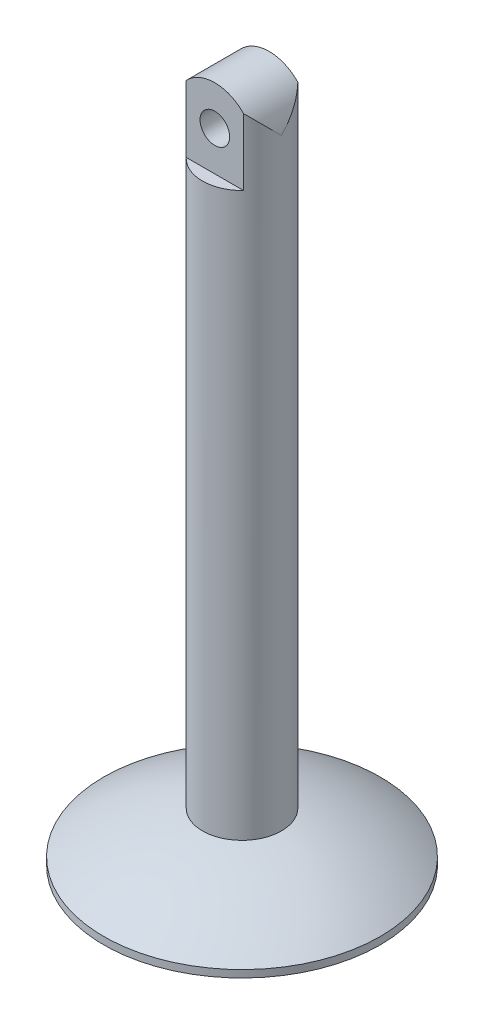
SolidWorks part; units mm, degrees
ref_plane "Front Plane" through (0, 0, 0) normal (0, 0, 1) x (1, 0, 0)
ref_plane "Top Plane" through (0, 0, 0) normal (0, 1, 0) x (1, 0, 0)
ref_plane "Right Plane" through (0, 0, 0) normal (1, 0, 0) x (0, 0, -1)
sketch "Sketch1" plane through (0, 0, 0) normal (0, 0, 1) x (1, 0, 0)
  line L0 (-14, -69.2598) -> (-14, -70)
  line L1 (0, 0) -> (-4, 0)
  line L2 (0, 0) -> (0, -65)
  line L3 (0, 0) -> (-4, 0)
  line L4 (-4, 0) -> (0, 0)
  line L5 (0, 0) -> (0, -65)
  line L6 (0, -65) -> (-4, -65)
  line L7 (-4, 0) -> (-4, -65)
  line L8 (0, -65) -> (-4, -65)
  line L9 (0, -65) -> (0, -70)
  line L10 (0, -70) -> (-14, -70)
  arc A0 (-14, -69.2598) -> (-4, -65) centre (0.9644, -90.5217) cw
  dimension "D4" = 5
  dimension "D3" = 26
  dimension "D6" = 14
  dimension "D1" = 4
  dimension "D2" = 0
  dimension "D5" = 0
  dimension "D8" = 65
revolve "Revolve1" add sketch "Sketch1" angle 360 about L2
sketch "Sketch2" plane through (0, 0, 0) normal (0, 0, 1) x (1, 0, 0)
  line L0 (4, 0) -> (-4, 0) construction
  line L1 (-4, -4) -> (4, -4)
  line L2 (-4, -4) -> (-4, 0)
  line L3 (-4, 0) -> (4, 0)
  line L4 (4, -4) -> (4, 0)
  circle A0 centre (0, -4) radius 4
  circle A1 centre (0, -4) radius 1.5
  dimension "D2" = 8
  dimension "D5" = 3
  dimension "D1" = 8
  dimension "D3" = 4
  dimension "D4" = 0
extrude "Cut-Extrude2" cut sketch "Sketch2" against normal through all both and the other way through all contours A0 L3 L2 | A0 L4 L3 | L1 A1 | L1 A1
sketch "Sketch3" plane through (0, 0, 0) normal (1, 0, 0) x (0, 0, -1)
  line L0 (4, 0) -> (-4, 0) construction
  line L1 (-2.75, 0) -> (2.75, 0)
  line L2 (-2.75, 0) -> (-2.75, -8)
  line L3 (-2.75, -8) -> (2.75, -8)
  line L4 (2.75, 0) -> (2.75, -8)
  line L5 (0, -4) -> (-4, 0) construction
  line L6 (-4, 0) -> (4, 0)
  line L7 (-4, 0) -> (-4, -8)
  line L8 (-4, -8) -> (4, -8)
  line L9 (4, 0) -> (4, -8)
  dimension "D1" = 8
  dimension "D2" = 0
  dimension "D3" = 2.75
  dimension "D4" = 5.5
  dimension "D5" = 1.25
  dimension "D6" = 1.25
  dimension "D7" = 8
extrude "Cut-Extrude3" cut sketch "Sketch3" against normal through all both and the other way through all contours L7 L8 L2 L6 | L9 L6 L4 L8
